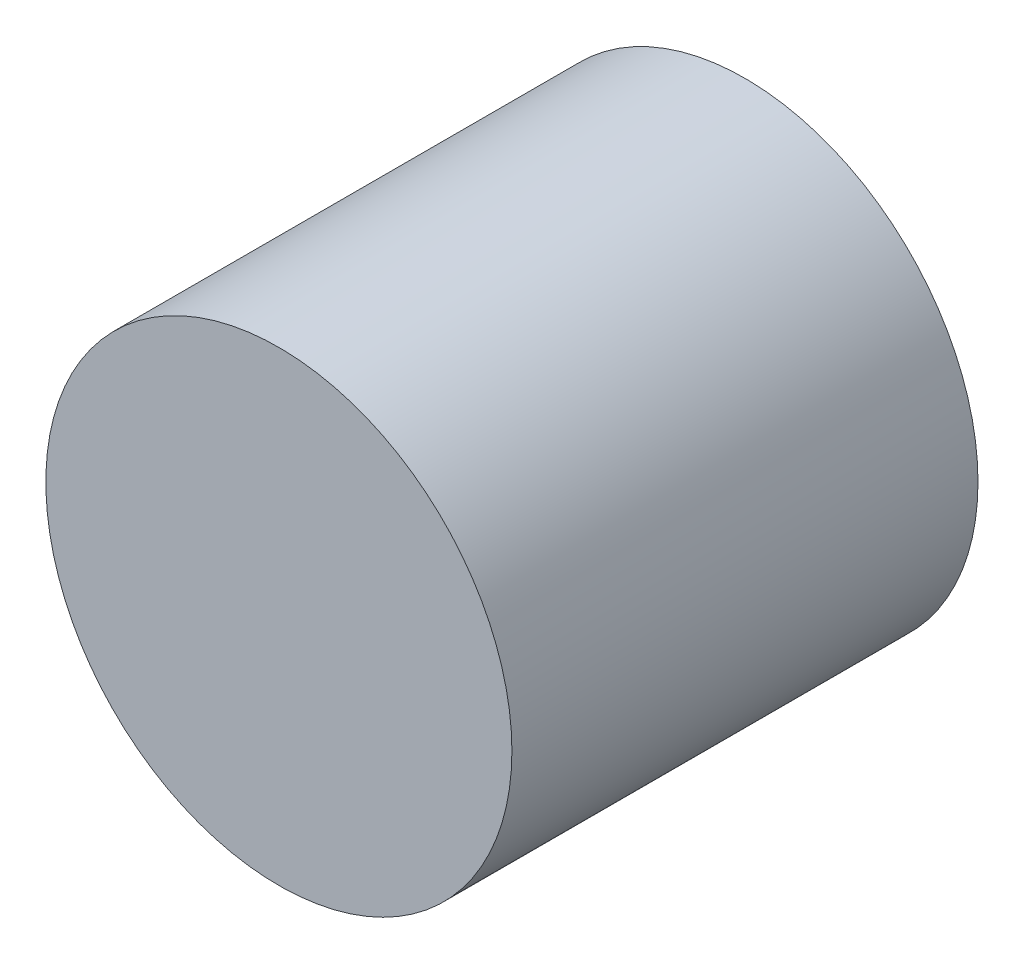
SolidWorks part; units mm, degrees
ref_plane "Front Plane" through (0, 0, 0) normal (0, 0, 1) x (1, 0, 0)
ref_plane "Top Plane" through (0, 0, 0) normal (0, 1, 0) x (1, 0, 0)
ref_plane "Right Plane" through (0, 0, 0) normal (1, 0, 0) x (0, 0, -1)
sketch "Sketch1" plane through (0, 0, 0) normal (0, 0, 1) x (1, 0, 0)
  circle A0 centre (0, 0) radius 3.175
  dimension "D1" = 6.35
extrude "Boss-Extrude1" add sketch "Sketch1" along normal blind 6.35
